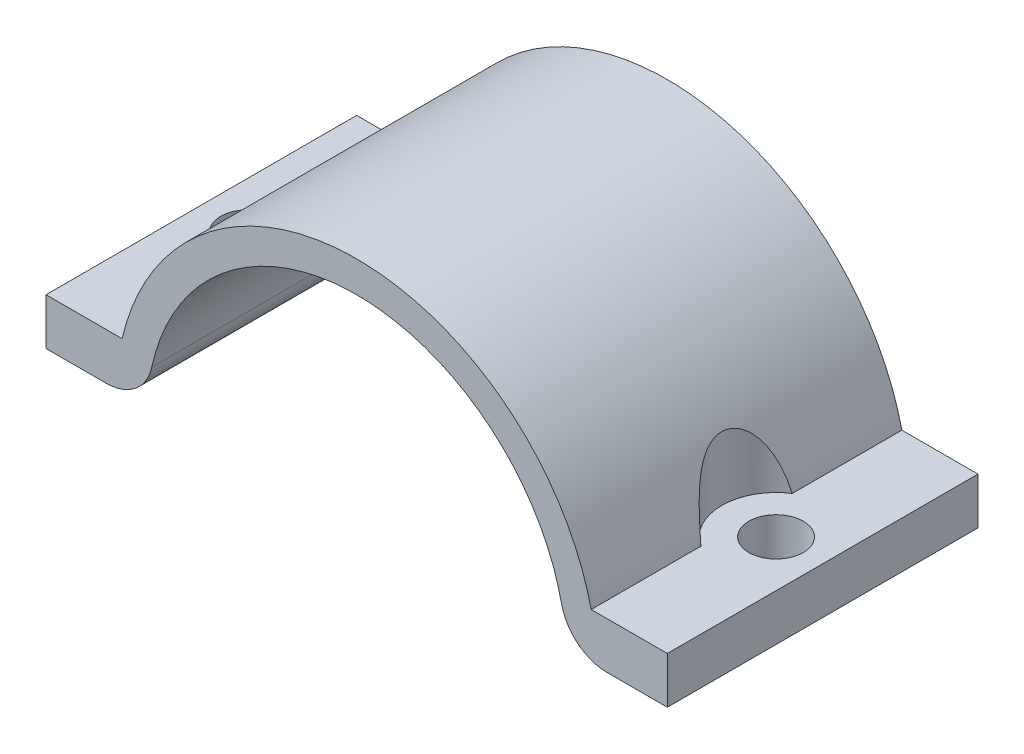
SolidWorks part; units mm, degrees
ref_plane "Plan de face" through (0, 0, 0) normal (0, 0, 1) x (1, 0, 0)
ref_plane "Plan de dessus" through (0, 0, 0) normal (0, 1, 0) x (1, 0, 0)
ref_plane "Plan de droite" through (0, 0, 0) normal (1, 0, 0) x (0, 0, -1)
sketch "Esquisse1" plane through (0, 0, 0) normal (0, 0, 1) x (1, 0, 0)
  line L0 (-14.2536, 0) -> (18.373, 0) construction
  line L1 (-20, 0.5) -> (-16.1245, 0.5)
  line L2 (-20, 0.5) -> (-20, 3.5)
  line L3 (-20, 3.5) -> (-15.0997, 3.5)
  line L4 (20, 0.5) -> (20, 3.5)
  line L5 (20, 3.5) -> (15.0997, 3.5)
  line L6 (16.1245, 0.5) -> (20, 0.5)
  arc A0 (15.0997, 3.5) -> (-15.0997, 3.5) centre (0, 0) ccw
  arc A1 (13.1928, 2.8636) -> (-13.1928, 2.8636) centre (0, 0) ccw
  arc A2 (16.1245, 0.5) -> (13.1928, 2.8636) centre (16.1245, 3.5) cw
  arc A3 (-13.1928, 2.8636) -> (-16.1245, 0.5) centre (-16.1245, 3.5) cw
  point P11 (0, 0)
  point P13 (0, 0)
  dimension "D1" = 27
  dimension "D2" = 2
  dimension "D7" = 3
  dimension "D3" = 1
  dimension "D4" = 3
  dimension "D5" = 40
  dimension "D6" = 20
extrude "Boss.-Extru.2" add sketch "Esquisse1" along normal blind 20
sketch "Esquisse3" plane through (0, 3.5, 0) normal (0, 1, 0) x (1, 0, 0)
  line L0 (-20, -20) -> (-20, 0) construction
  circle A0 centre (-17, -10) radius 1.75
  circle A1 centre (17, -10) radius 1.75
  point P6 (-20, -10)
  dimension "D1" = 3.5
  dimension "D2" = 34
  dimension "D3" = 17
extrude "Enlèv. mat.-Extru.2" cut sketch "Esquisse3" against normal through all
sketch "Esquisse4" plane through (0, 3.5, 0) normal (0, 1, 0) x (1, 0, 0)
  circle A0 centre (-17, -10) radius 3.5
  circle A1 centre (17, -10) radius 3.5
  dimension "D1" = 7
extrude "Enlèv. mat.-Extru.3" cut sketch "Esquisse4" along normal through all
